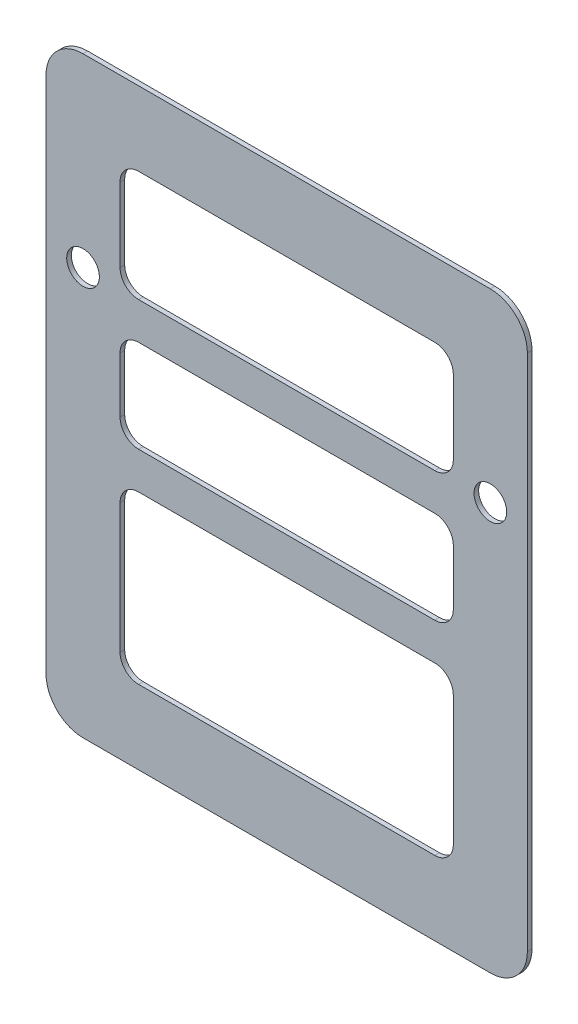
SolidWorks part; units mm, degrees
material "McMaster Carbon Fiber Twill Tube"
ref_plane "Front Plane" through (0, 0, 0) normal (0, 0, 1) x (1, 0, 0)
ref_plane "Top Plane" through (0, 0, 0) normal (0, 1, 0) x (1, 0, 0)
ref_plane "Right Plane" through (0, 0, 0) normal (1, 0, 0) x (0, 0, -1)
sketch "Sketch1" plane through (0, 0, 0) normal (0, 0, 1) x (1, 0, 0)
  line L0 (-165.1, 76.2) -> (-139.7, 76.2) construction
  line L1 (-139.7, -203.2) -> (139.7, -203.2)
  line L2 (-165.1, -177.8) -> (-165.1, 177.8)
  line L3 (-139.7, 203.2) -> (139.7, 203.2)
  line L4 (165.1, -177.8) -> (165.1, 177.8)
  line L5 (-165.1, -203.2) -> (165.1, 203.2) construction
  line L6 (-165.1, 203.2) -> (165.1, -203.2) construction
  line L7 (-139.7, 76.2) -> (139.7, 76.2) construction
  line L8 (139.7, 76.2) -> (165.1, 76.2) construction
  line L10 (-101.6, -152.4) -> (101.6, -152.4)
  line L11 (-114.3, -139.7) -> (-114.3, -50.8)
  line L12 (-101.6, -38.1) -> (101.6, -38.1)
  line L13 (114.3, -139.7) -> (114.3, -50.8)
  line L14 (-101.6, -12.7) -> (101.6, -12.7)
  line L15 (-114.3, 0) -> (-114.3, 38.1)
  line L16 (-101.6, 50.8) -> (101.6, 50.8)
  line L17 (114.3, 0) -> (114.3, 38.1)
  line L18 (-101.6, 152.4) -> (101.6, 152.4)
  line L19 (-114.3, 139.7) -> (-114.3, 88.9)
  line L20 (-101.6, 76.2) -> (101.6, 76.2)
  line L21 (114.3, 139.7) -> (114.3, 88.9)
  circle A0 centre (-139.7, 76.2) radius 11.2
  circle A1 centre (139.7, 76.2) radius 11.2
  arc A2 (-139.7, -203.2) -> (-165.1, -177.8) centre (-139.7, -177.8) cw
  arc A3 (139.7, -203.2) -> (165.1, -177.8) centre (139.7, -177.8) ccw
  arc A4 (139.7, 203.2) -> (165.1, 177.8) centre (139.7, 177.8) cw
  arc A5 (-165.1, 177.8) -> (-139.7, 203.2) centre (-139.7, 177.8) cw
  arc A6 (-114.3, -50.8) -> (-101.6, -38.1) centre (-101.6, -50.8) cw
  arc A7 (-101.6, -152.4) -> (-114.3, -139.7) centre (-101.6, -139.7) cw
  arc A8 (101.6, -152.4) -> (114.3, -139.7) centre (101.6, -139.7) ccw
  arc A9 (101.6, -38.1) -> (114.3, -50.8) centre (101.6, -50.8) cw
  arc A10 (101.6, -12.7) -> (114.3, 0) centre (101.6, 0) ccw
  arc A11 (-101.6, -12.7) -> (-114.3, 0) centre (-101.6, 0) cw
  arc A12 (-114.3, 38.1) -> (-101.6, 50.8) centre (-101.6, 38.1) cw
  arc A13 (101.6, 50.8) -> (114.3, 38.1) centre (101.6, 38.1) cw
  arc A14 (101.6, 76.2) -> (114.3, 88.9) centre (101.6, 88.9) ccw
  arc A15 (101.6, 152.4) -> (114.3, 139.7) centre (101.6, 139.7) cw
  arc A16 (-101.6, 152.4) -> (-114.3, 139.7) centre (-101.6, 139.7) ccw
  arc A17 (-114.3, 88.9) -> (-101.6, 76.2) centre (-101.6, 88.9) ccw
  point P0 (0, 0)
  point P40 (-114.3, -38.1)
  point P45 (114.3, -152.4)
  point P48 (114.3, -38.1)
  point P51 (114.3, -12.7)
  point P54 (-114.3, -12.7)
  point P57 (-114.3, 50.8)
  point P60 (114.3, 50.8)
  point P63 (114.3, 76.2)
  point P70 (-114.3, 76.2)
  dimension "D3" = 22.4
  dimension "D6" = 25.4
  dimension "D15" = 12.7
  dimension "D1" = 406.4
  dimension "D2" = 330.2
  dimension "D4" = 279.4
  dimension "D5" = 127
  dimension "D7" = 50.8
  dimension "D8" = 50.8
  dimension "D9" = 50.8
  dimension "D10" = 114.3
  dimension "D11" = 25.4
  dimension "D12" = 63.5
  dimension "D13" = 50.8
  dimension "D14" = 76.2
extrude "Boss-Extrude1" add sketch "Sketch1" along normal blind 3.175
